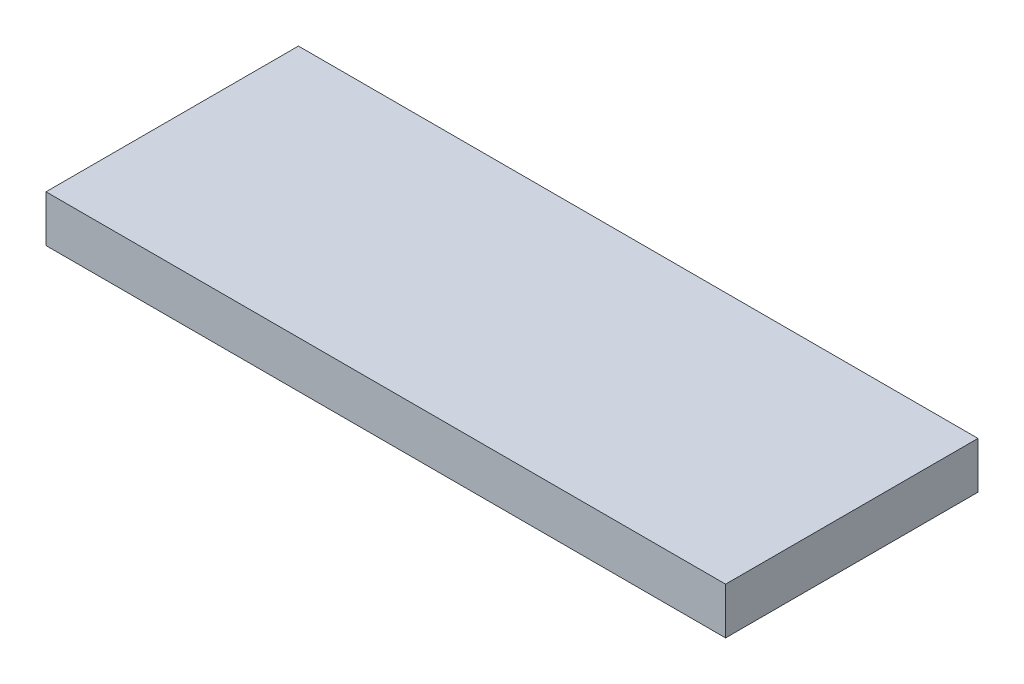
SolidWorks part; units mm, degrees
ref_plane "Front Plane" through (0, 0, 0) normal (0, 0, 1) x (1, 0, 0)
ref_plane "Top Plane" through (0, 0, 0) normal (0, 1, 0) x (1, 0, 0)
ref_plane "Right Plane" through (0, 0, 0) normal (1, 0, 0) x (0, 0, -1)
sketch "Sketch2" plane through (0, 0, 0) normal (0, 1, 0) x (1, 0, 0)
  line L1 (-64.3689, -26.2317) -> (110.6311, -26.2317)
  line L2 (-64.3689, -26.2317) -> (-64.3689, 38.7683)
  line L3 (-64.3689, 38.7683) -> (110.6311, 38.7683)
  line L4 (110.6311, -26.2317) -> (110.6311, 38.7683)
  dimension "D1" = 65
  dimension "D2" = 175
extrude "Boss-Extrude1" add sketch "Sketch2" along normal blind 12
